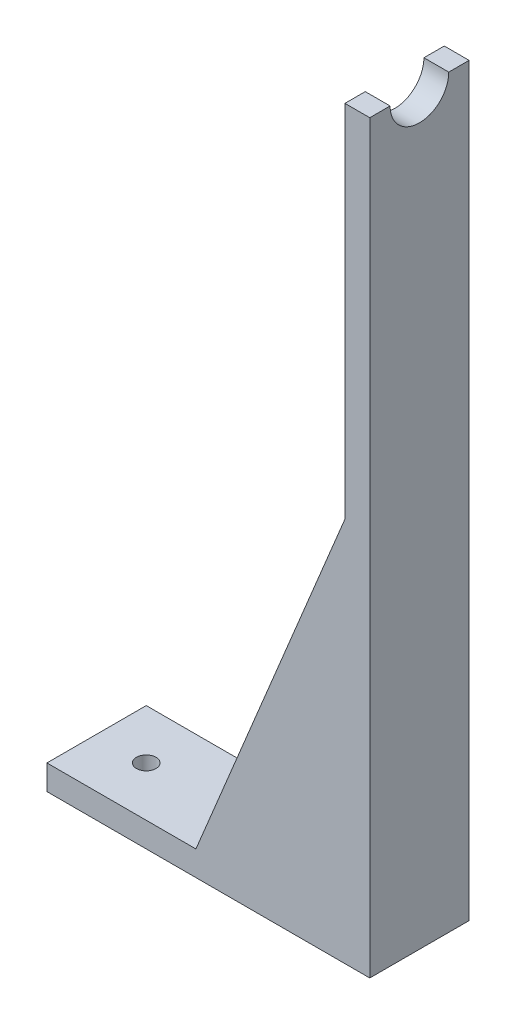
SolidWorks part; units mm, degrees
ref_plane "Front Plane" through (0, 0, 0) normal (0, 0, 1) x (1, 0, 0)
ref_plane "Top Plane" through (0, 0, 0) normal (0, 1, 0) x (1, 0, 0)
ref_plane "Right Plane" through (0, 0, 0) normal (1, 0, 0) x (0, 0, -1)
sketch "Sketch2" plane through (0, 0, 0) normal (0, 1, 0) x (1, 0, 0)
  line L1 (38.1, -12.7) -> (-38.1, -12.7)
  line L2 (38.1, -12.7) -> (38.1, 12.7)
  line L3 (38.1, 12.7) -> (-38.1, 12.7)
  line L4 (-38.1, -12.7) -> (-38.1, 12.7)
  line L5 (38.1, -12.7) -> (-38.1, 12.7) construction
  line L6 (38.1, 12.7) -> (-38.1, -12.7) construction
  circle A0 centre (-25.4, 0) radius 2.5
  circle A1 centre (25.4, 0) radius 2.5
  point P0 (0, 0)
  point P10 (-25.4, 0)
  point P11 (0, 0)
  point P12 (0, 0)
  dimension "D3" = 5
  dimension "D1" = 25.4
  dimension "D2" = 76.2
  dimension "D4" = 12.7
  dimension "D5" = 12.7
extrude "Boss-Extrude1" add sketch "Sketch2" along normal blind 6.35
sketch "Sketch3" plane through (38.1, 0, 0) normal (1, 0, 0) x (0, 0, -1)
  line L0 (12.7, 6.35) -> (12.7, 0) construction
  line L1 (-12.7, 0) -> (12.7, 0)
  line L2 (-12.7, 0) -> (-12.7, 190.5)
  line L3 (-12.7, 190.5) -> (12.7, 190.5)
  line L4 (12.7, 0) -> (12.7, 190.5)
  line L5 (-12.7, 0) -> (12.7, 190.5) construction
  line L6 (-12.7, 190.5) -> (12.7, 0) construction
  point P4 (0, 95.25)
  dimension "D1" = 190.5
extrude "Boss-Extrude2" add sketch "Sketch3" along normal blind 6.35
sketch "Sketch4" plane through (0, 0, 12.7) normal (0, 0, 1) x (1, 0, 0)
  line L0 (27.9, 6.35) -> (22.9, 6.35) construction
  line L1 (-22.9, 6.35) -> (-27.9, 6.35) construction
  line L2 (27.9, 6.35) -> (22.9, 6.35)
  line L3 (-22.9, 6.35) -> (-27.9, 6.35)
  line L4 (-25.4, 6.35) -> (25.4, 6.35) construction
  line L5 (0, 6.35) -> (38.1, 98.425)
  line L6 (38.1, 190.5) -> (38.1, 6.35) construction
  line L7 (0, 6.35) -> (38.1, 6.35)
  line L8 (38.1, 6.35) -> (38.1, 98.425)
  line M4 (38.1, 190.5) -> (38.1, 6.35)
  line M5 (38.1, 6.35) -> (-38.1, 6.35)
extrude "Boss-Extrude3" add sketch "Sketch4" against normal blind 5.08 separate body contours L5 L7 M5 M4
mirror "Mirror2" about plane through (0, 0, 0) normal (0, 0, 1) of bodies 103
combine bodies "Combine1" operation type add bodies to combine 103 104 102
sketch "Sketch5" plane through (44.45, 0, 0) normal (1, 0, 0) x (0, 0, -1)
  line L0 (12.7, 190.5) -> (-12.7, 190.5) construction
  circle A0 centre (0, 190.5) radius 7.5
  dimension "D1" = 15
extrude "Cut-Extrude1" cut sketch "Sketch5" against normal blind 37.592
